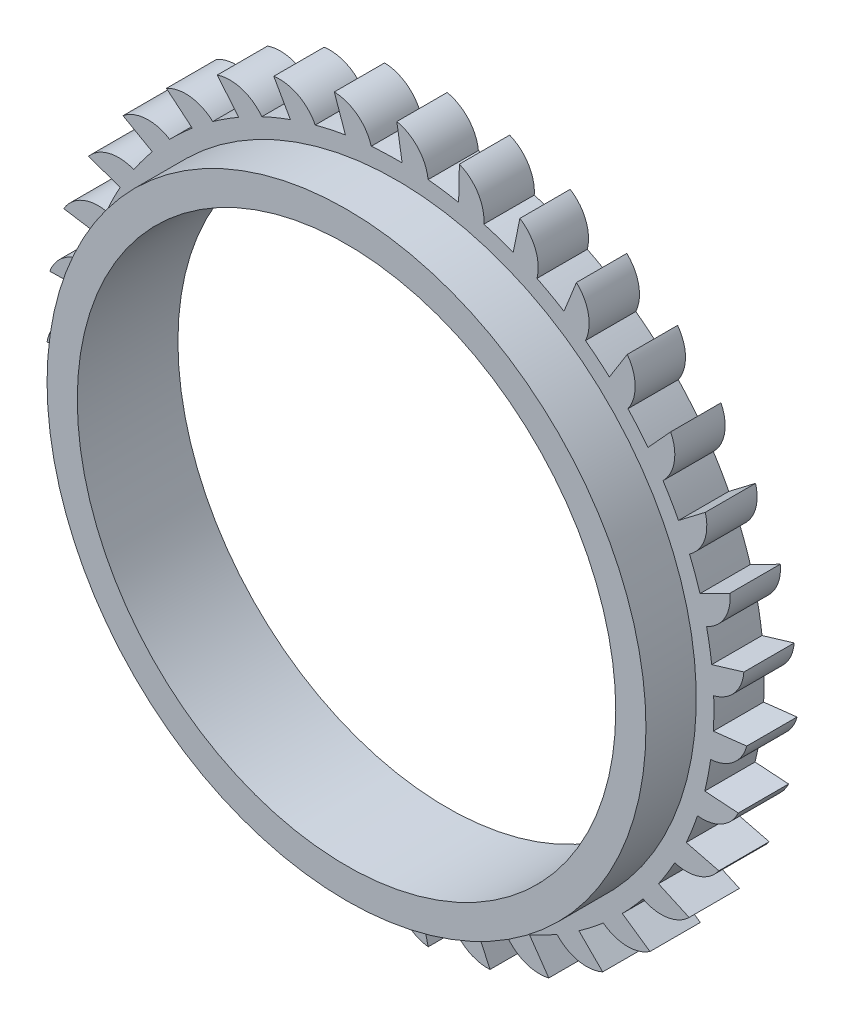
SolidWorks part; units mm, degrees
ref_plane "Front Plane" through (0, 0, 0) normal (0, 0, 1) x (1, 0, 0)
ref_plane "Top Plane" through (0, 0, 0) normal (0, 1, 0) x (1, 0, 0)
ref_plane "Right Plane" through (0, 0, 0) normal (1, 0, 0) x (0, 0, -1)
sketch "Sketch1" plane through (0, 0, 0) normal (0, 0, 1) x (1, 0, 0)
  line L0 (0, 0) -> (0, 86.2477) construction
  line L1 (0, 69.588) -> (1.0486, 62.9913)
  line L2 (12.4254, 68.4697) -> (12.2793, 61.7917)
  line L3 (24.4515, 65.1507) -> (23.1153, 58.6062)
  line L4 (35.6916, 59.7377) -> (33.2084, 53.5369)
  line L5 (45.7846, 52.4047) -> (42.2341, 46.747)
  line L6 (54.4061, 43.3874) -> (49.9024, 38.4546)
  line L7 (61.2789, 32.9756) -> (55.9667, 28.9262)
  line L8 (66.1821, 21.5039) -> (60.2323, 18.4681)
  line L9 (68.9582, 9.341) -> (62.5619, 7.4164)
  line L10 (69.5179, -3.1221) -> (62.8808, -3.8736)
  line L11 (67.8433, -15.4848) -> (61.1786, -15.0392)
  line L12 (63.9881, -27.3498) -> (57.5101, -25.7214)
  line L13 (58.0763, -38.3358) -> (51.9932, -35.5768)
  line L14 (50.2979, -48.0897) -> (44.8051, -44.2888)
  line L15 (40.9028, -56.2979) -> (36.177, -51.5774)
  line L16 (30.1931, -62.6966) -> (26.3861, -57.2082)
  line L17 (18.513, -67.0803) -> (15.7472, -61.0002)
  line L18 (6.2378, -69.3079) -> (4.6021, -62.8317)
  line L19 (-6.2378, -69.3079) -> (-6.6909, -62.6437)
  line L20 (-18.513, -67.0803) -> (-17.7688, -60.4423)
  line L21 (-30.1931, -62.6966) -> (-28.2757, -56.2982)
  line L22 (-40.9028, -56.2979) -> (-37.8737, -50.3447)
  line L23 (-50.2979, -48.0897) -> (-46.2544, -42.773)
  line L24 (-58.0763, -38.3358) -> (-53.1485, -33.8266)
  line L25 (-63.9881, -27.3498) -> (-58.3344, -23.7929)
  line L26 (-67.8433, -15.4848) -> (-61.6453, -12.9946)
  line L27 (-69.5179, -3.1221) -> (-62.9749, -1.7785)
  line L28 (-68.9582, 9.341) -> (-62.2804, 9.4946)
  line L29 (-66.1821, 21.5039) -> (-59.5842, 20.4627)
  line L30 (-61.2789, 32.9756) -> (-54.9729, 30.773)
  line L31 (-54.4061, 43.3874) -> (-48.5948, 40.0943)
  line L32 (-45.7846, 52.4047) -> (-40.6547, 48.1269)
  line L33 (-35.6916, 59.7377) -> (-31.408, 54.6126)
  line L34 (-24.4515, 65.1507) -> (-21.1518, 59.3431)
  line L35 (-12.4254, 68.4697) -> (-10.2158, 62.1662)
  arc A0 (12.2793, 61.7917) -> (6.2076, 62.6934) centre (0, 0) ccw
  arc A1 (0, 69.588) -> (6.2076, 62.6934) centre (-1.6604, 61.8512) cw
  arc A2 (12.4254, 68.4697) -> (17.3022, 60.5775) centre (9.4102, 61.1537) cw
  arc A3 (24.4515, 65.1507) -> (27.8407, 56.5146) centre (20.1784, 58.4907) cw
  arc A4 (35.6916, 59.7377) -> (37.4843, 50.6352) centre (30.298, 53.9477) cw
  arc A5 (45.7846, 52.4047) -> (45.9232, 43.1284) centre (39.4439, 47.6708) cw
  arc A6 (54.4061, 43.3874) -> (52.8861, 34.2354) centre (47.3219, 39.8618) cw
  arc A7 (61.2789, 32.9756) -> (58.1491, 24.242) centre (53.679, 30.7715) cw
  arc A8 (66.1821, 21.5039) -> (61.5433, 13.4695) centre (58.3109, 20.6922) cw
  arc A9 (68.9582, 9.341) -> (62.9593, 2.2641) centre (61.0685, 9.9479) cw
  arc A10 (69.5179, -3.1221) -> (62.3518, -9.0141) centre (61.8634, -1.1162) cw
  arc A11 (67.8433, -15.4848) -> (59.7402, -20.0026) centre (60.6699, -12.1444) cw
  arc A12 (63.9881, -27.3498) -> (55.2086, -30.3482) centre (57.5265, -22.7822) cw
  arc A13 (58.0763, -38.3358) -> (48.9025, -39.7183) centre (52.5341, -32.6879) cw
  arc A14 (50.2979, -48.0897) -> (41.0246, -47.8119) centre (45.8532, -41.5429) cw
  arc A15 (40.9028, -56.2979) -> (31.8282, -54.3688) centre (37.6985, -49.0627) cw
  arc A16 (30.1931, -62.6966) -> (21.6088, -59.1782) centre (28.3322, -55.0055) cw
  arc A17 (18.513, -67.0803) -> (10.6948, -62.0856) centre (18.0553, -59.1805) cw
  arc A18 (6.2378, -69.3079) -> (-0.5628, -62.9975) centre (7.198, -61.4533) cw
  arc A19 (-6.2378, -69.3079) -> (-11.8024, -61.8846) centre (-3.8906, -61.751) cw
  arc A20 (-18.513, -67.0803) -> (-22.6627, -58.7827) centre (-14.8541, -60.064) cw
  arc A21 (-30.1931, -62.6966) -> (-32.7945, -53.7914) centre (-25.3402, -56.4464) cw
  arc A22 (-40.9028, -56.2979) -> (-41.8723, -47.0713) centre (-35.0119, -51.0146) cw
  arc A23 (-50.2979, -48.0897) -> (-49.6043, -38.8382) centre (-43.5583, -43.9432) cw
  arc A24 (-58.0763, -38.3358) -> (-55.742, -29.3569) centre (-50.7046, -35.4594) cw
  arc A25 (-63.9881, -27.3498) -> (-60.0881, -18.932) centre (-56.2213, -25.8359) cw
  arc A26 (-67.8433, -15.4848) -> (-62.5029, -7.8986) centre (-59.931, -15.382) cw
  arc A27 (-69.5179, -3.1221) -> (-62.9088, 3.3886) centre (-61.7144, -4.4337) cw
  arc A28 (-68.9582, 9.341) -> (-61.2928, 14.567) centre (-61.5143, 6.6571) cw
  arc A29 (-66.1821, 21.5039) -> (-57.7067, 25.2771) centre (-59.3371, 17.5339) cw
  arc A30 (-61.2789, 32.9756) -> (-52.2659, 35.1749) centre (-55.2527, 27.8472) cw
  arc A31 (-54.4061, 43.3874) -> (-45.1453, 43.942) centre (-49.3925, 37.2654) cw
  arc A32 (-45.7846, 52.4047) -> (-36.5736, 51.2969) centre (-41.9447, 45.4859) cw
  arc A33 (-35.6916, 59.7377) -> (-26.8265, 57.003) centre (-33.1488, 52.2444) cw
  arc A34 (-24.4515, 65.1507) -> (-16.2171, 60.877) centre (-23.2875, 57.3238) cw
  arc A35 (-12.4254, 68.4697) -> (-5.0865, 62.7943) centre (-12.6777, 60.5607) cw
  arc A36 (1.0486, 62.9913) -> (-5.0865, 62.7943) centre (0, 0) ccw
  arc A37 (23.1153, 58.6062) -> (17.3022, 60.5775) centre (0, 0) ccw
  arc A38 (33.2084, 53.5369) -> (27.8407, 56.5146) centre (0, 0) ccw
  arc A39 (42.2341, 46.747) -> (37.4843, 50.6352) centre (0, 0) ccw
  arc A40 (49.9024, 38.4546) -> (45.9232, 43.1284) centre (0, 0) ccw
  arc A41 (55.9667, 28.9262) -> (52.8861, 34.2354) centre (0, 0) ccw
  arc A42 (60.2323, 18.4681) -> (58.1491, 24.242) centre (0, 0) ccw
  arc A43 (62.5619, 7.4164) -> (61.5433, 13.4695) centre (0, 0) ccw
  arc A44 (62.8808, -3.8736) -> (62.9593, 2.2641) centre (0, 0) ccw
  arc A45 (61.1786, -15.0392) -> (62.3518, -9.0141) centre (0, 0) ccw
  arc A46 (57.5101, -25.7214) -> (59.7402, -20.0026) centre (0, 0) ccw
  arc A47 (51.9932, -35.5768) -> (55.2086, -30.3482) centre (0, 0) ccw
  arc A48 (44.8051, -44.2888) -> (48.9025, -39.7183) centre (0, 0) ccw
  arc A49 (36.177, -51.5774) -> (41.0246, -47.8119) centre (0, 0) ccw
  arc A50 (26.3861, -57.2082) -> (31.8282, -54.3688) centre (0, 0) ccw
  arc A51 (15.7472, -61.0002) -> (21.6088, -59.1782) centre (0, 0) ccw
  arc A52 (4.6021, -62.8317) -> (10.6948, -62.0856) centre (0, 0) ccw
  arc A53 (-6.6909, -62.6437) -> (-0.5628, -62.9975) centre (0, 0) ccw
  arc A54 (-17.7688, -60.4423) -> (-11.8024, -61.8846) centre (0, 0) ccw
  arc A55 (-28.2757, -56.2982) -> (-22.6627, -58.7827) centre (0, 0) ccw
  arc A56 (-37.8737, -50.3447) -> (-32.7945, -53.7914) centre (0, 0) ccw
  arc A57 (-46.2544, -42.773) -> (-41.8723, -47.0713) centre (0, 0) ccw
  arc A58 (-53.1485, -33.8266) -> (-49.6043, -38.8382) centre (0, 0) ccw
  arc A59 (-58.3344, -23.7929) -> (-55.742, -29.3569) centre (0, 0) ccw
  arc A60 (-61.6453, -12.9946) -> (-60.0881, -18.932) centre (0, 0) ccw
  arc A61 (-62.9749, -1.7785) -> (-62.5029, -7.8986) centre (0, 0) ccw
  arc A62 (-62.2804, 9.4946) -> (-62.9088, 3.3886) centre (0, 0) ccw
  arc A63 (-59.5842, 20.4627) -> (-61.2928, 14.567) centre (0, 0) ccw
  arc A64 (-54.9729, 30.773) -> (-57.7067, 25.2771) centre (0, 0) ccw
  arc A65 (-48.5948, 40.0943) -> (-52.2659, 35.1749) centre (0, 0) ccw
  arc A66 (-40.6547, 48.1269) -> (-45.1453, 43.942) centre (0, 0) ccw
  arc A67 (-31.408, 54.6126) -> (-36.5736, 51.2969) centre (0, 0) ccw
  arc A68 (-21.1518, 59.3431) -> (-26.8265, 57.003) centre (0, 0) ccw
  arc A69 (-10.2158, 62.1662) -> (-16.2171, 60.877) centre (0, 0) ccw
  point P147 (0, 0)
  dimension "D1" = 126
  dimension "D2" = 35
extrude "Boss-Extrude1" add sketch "Sketch1" along normal blind 10
sketch "Sketch2" plane through (0, 0, 10) normal (0, 0, 1) x (1, 0, 0)
  circle A0 centre (0, 0) radius 59.5
  circle A1 centre (0, 0) radius 53.5
  dimension "D1" = 119
  dimension "D2" = 107
extrude "Boss-Extrude2" add sketch "Sketch2" along normal blind 10
sketch "Sketch3" plane through (0, 0, 10) normal (0, 0, 1) x (1, 0, 0)
  circle A0 centre (0, 0) radius 53.5
  dimension "D1" = 107
extrude "Cut-Extrude4" cut sketch "Sketch3" against normal blind 10
